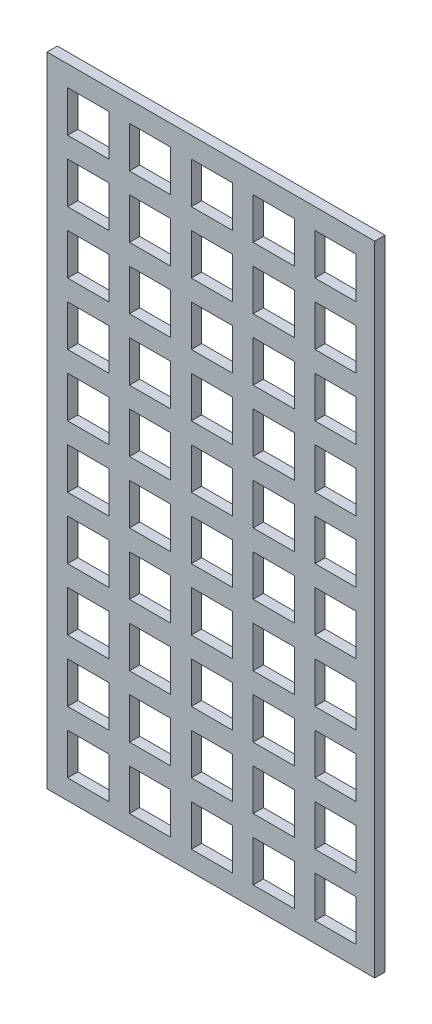
SolidWorks part; units mm, degrees
ref_plane "Front Plane" through (0, 0, 0) normal (0, 0, 1) x (1, 0, 0)
ref_plane "Top Plane" through (0, 0, 0) normal (0, 1, 0) x (1, 0, 0)
ref_plane "Right Plane" through (0, 0, 0) normal (1, 0, 0) x (0, 0, -1)
sketch "Sketch1" plane through (0, 0, 0) normal (0, 0, 1) x (1, 0, 0)
  line L0 (0, 0) -> (0, -5)
  line L1 (0, 0) -> (79.5, 0)
  line L2 (0, 0) -> (0, -154.8)
  line L3 (0, -154.8) -> (79.5, -154.8)
  line L4 (79.5, 0) -> (79.5, -154.8)
  line L5 (5, -5) -> (0, -5) construction
  line L6 (0, -5) -> (5, -5) construction
  line L7 (5, 0) -> (5, -5) construction
  line L8 (20, 0) -> (20, -5) construction
  line L9 (5, -5) -> (15, -5)
  line L10 (20, -15) -> (30, -15)
  line L11 (20, -15) -> (20, -5)
  line L12 (5, -15) -> (5, -5)
  line L13 (5, -15) -> (5, -5)
  line L14 (5, -5) -> (15, -5)
  line L15 (5, -5) -> (5, -15)
  line L16 (5, -15) -> (15, -15)
  line L17 (15, -5) -> (15, -15)
  line L18 (5, -5) -> (15, -5)
  line L19 (20, -5) -> (30, -5)
  line L20 (30, -5) -> (30, -15)
  line L21 (35, 0) -> (35, -5) construction
  line L22 (35, -15) -> (45, -15)
  line L23 (35, -15) -> (35, -5)
  line L24 (35, -5) -> (45, -5)
  line L25 (45, -5) -> (45, -15)
  line L26 (50, 0) -> (50, -5) construction
  line L27 (50, -15) -> (60, -15)
  line L28 (50, -15) -> (50, -5)
  line L29 (50, -5) -> (60, -5)
  line L30 (60, -5) -> (60, -15)
  line L31 (65, 0) -> (65, -5) construction
  line L32 (65, -15) -> (75, -15)
  line L33 (65, -15) -> (65, -5)
  line L34 (65, -5) -> (75, -5)
  line L35 (75, -5) -> (75, -15)
  line L36 (20, -15) -> (20, -20) construction
  line L37 (20, -30) -> (30, -30)
  line L38 (20, -30) -> (20, -20)
  line L39 (20, -20) -> (30, -20)
  line L40 (30, -20) -> (30, -30)
  line L41 (35, -15) -> (35, -20) construction
  line L42 (35, -30) -> (45, -30)
  line L43 (35, -30) -> (35, -20)
  line L44 (35, -20) -> (45, -20)
  line L45 (45, -20) -> (45, -30)
  line L46 (50, -15) -> (50, -20) construction
  line L47 (50, -30) -> (60, -30)
  line L48 (50, -30) -> (50, -20)
  line L49 (50, -20) -> (60, -20)
  line L50 (60, -20) -> (60, -30)
  line L51 (65, -15) -> (65, -20) construction
  line L52 (65, -30) -> (75, -30)
  line L53 (65, -30) -> (65, -20)
  line L54 (65, -20) -> (75, -20)
  line L55 (75, -20) -> (75, -30)
  line L56 (20, -30) -> (20, -35) construction
  line L57 (20, -45) -> (30, -45)
  line L58 (20, -45) -> (20, -35)
  line L59 (20, -35) -> (30, -35)
  line L60 (30, -35) -> (30, -45)
  line L61 (35, -30) -> (35, -35) construction
  line L62 (35, -45) -> (45, -45)
  line L63 (35, -45) -> (35, -35)
  line L64 (35, -35) -> (45, -35)
  line L65 (45, -35) -> (45, -45)
  line L66 (50, -30) -> (50, -35) construction
  line L67 (50, -45) -> (60, -45)
  line L68 (50, -45) -> (50, -35)
  line L69 (50, -35) -> (60, -35)
  line L70 (60, -35) -> (60, -45)
  line L71 (65, -30) -> (65, -35) construction
  line L72 (65, -45) -> (75, -45)
  line L73 (65, -45) -> (65, -35)
  line L74 (65, -35) -> (75, -35)
  line L75 (75, -35) -> (75, -45)
  line L76 (20, -45) -> (20, -50) construction
  line L77 (20, -60) -> (30, -60)
  line L78 (20, -60) -> (20, -50)
  line L79 (20, -50) -> (30, -50)
  line L80 (30, -50) -> (30, -60)
  line L81 (35, -45) -> (35, -50) construction
  line L82 (35, -60) -> (45, -60)
  line L83 (35, -60) -> (35, -50)
  line L84 (35, -50) -> (45, -50)
  line L85 (45, -50) -> (45, -60)
  line L86 (50, -45) -> (50, -50) construction
  line L87 (50, -60) -> (60, -60)
  line L88 (50, -60) -> (50, -50)
  line L89 (50, -50) -> (60, -50)
  line L90 (60, -50) -> (60, -60)
  line L91 (65, -45) -> (65, -50) construction
  line L92 (65, -60) -> (75, -60)
  line L93 (65, -60) -> (65, -50)
  line L94 (65, -50) -> (75, -50)
  line L95 (75, -50) -> (75, -60)
  line L96 (20, -60) -> (20, -65) construction
  line L97 (20, -75) -> (30, -75)
  line L98 (20, -75) -> (20, -65)
  line L99 (20, -65) -> (30, -65)
  line L100 (30, -65) -> (30, -75)
  line L101 (35, -60) -> (35, -65) construction
  line L102 (35, -75) -> (45, -75)
  line L103 (35, -75) -> (35, -65)
  line L104 (35, -65) -> (45, -65)
  line L105 (45, -65) -> (45, -75)
  line L106 (50, -60) -> (50, -65) construction
  line L107 (50, -75) -> (60, -75)
  line L108 (50, -75) -> (50, -65)
  line L109 (50, -65) -> (60, -65)
  line L110 (60, -65) -> (60, -75)
  line L111 (65, -60) -> (65, -65) construction
  line L112 (65, -75) -> (75, -75)
  line L113 (65, -75) -> (65, -65)
  line L114 (65, -65) -> (75, -65)
  line L115 (75, -65) -> (75, -75)
  line L116 (20, -75) -> (20, -80) construction
  line L117 (20, -90) -> (30, -90)
  line L118 (20, -90) -> (20, -80)
  line L119 (20, -80) -> (30, -80)
  line L120 (30, -80) -> (30, -90)
  line L121 (35, -75) -> (35, -80) construction
  line L122 (35, -90) -> (45, -90)
  line L123 (35, -90) -> (35, -80)
  line L124 (35, -80) -> (45, -80)
  line L125 (45, -80) -> (45, -90)
  line L126 (50, -75) -> (50, -80) construction
  line L127 (50, -90) -> (60, -90)
  line L128 (50, -90) -> (50, -80)
  line L129 (50, -80) -> (60, -80)
  line L130 (60, -80) -> (60, -90)
  line L131 (65, -75) -> (65, -80) construction
  line L132 (65, -90) -> (75, -90)
  line L133 (65, -90) -> (65, -80)
  line L134 (65, -80) -> (75, -80)
  line L135 (75, -80) -> (75, -90)
  line L136 (20, -90) -> (20, -95) construction
  line L137 (20, -105) -> (30, -105)
  line L138 (20, -105) -> (20, -95)
  line L139 (20, -95) -> (30, -95)
  line L140 (30, -95) -> (30, -105)
  line L141 (35, -90) -> (35, -95) construction
  line L142 (35, -105) -> (45, -105)
  line L143 (35, -105) -> (35, -95)
  line L144 (35, -95) -> (45, -95)
  line L145 (45, -95) -> (45, -105)
  line L146 (50, -90) -> (50, -95) construction
  line L147 (50, -105) -> (60, -105)
  line L148 (50, -105) -> (50, -95)
  line L149 (50, -95) -> (60, -95)
  line L150 (60, -95) -> (60, -105)
  line L151 (65, -90) -> (65, -95) construction
  line L152 (65, -105) -> (75, -105)
  line L153 (65, -105) -> (65, -95)
  line L154 (65, -95) -> (75, -95)
  line L155 (75, -95) -> (75, -105)
  line L156 (20, -105) -> (20, -110) construction
  line L157 (20, -120) -> (30, -120)
  line L158 (20, -120) -> (20, -110)
  line L159 (20, -110) -> (30, -110)
  line L160 (30, -110) -> (30, -120)
  line L161 (35, -105) -> (35, -110) construction
  line L162 (35, -120) -> (45, -120)
  line L163 (35, -120) -> (35, -110)
  line L164 (35, -110) -> (45, -110)
  line L165 (45, -110) -> (45, -120)
  line L166 (50, -105) -> (50, -110) construction
  line L167 (50, -120) -> (60, -120)
  line L168 (50, -120) -> (50, -110)
  line L169 (50, -110) -> (60, -110)
  line L170 (60, -110) -> (60, -120)
  line L171 (65, -105) -> (65, -110) construction
  line L172 (65, -120) -> (75, -120)
  line L173 (65, -120) -> (65, -110)
  line L174 (65, -110) -> (75, -110)
  line L175 (75, -110) -> (75, -120)
  line L176 (20, -120) -> (20, -125) construction
  line L177 (20, -135) -> (30, -135)
  line L178 (20, -135) -> (20, -125)
  line L179 (20, -125) -> (30, -125)
  line L180 (30, -125) -> (30, -135)
  line L181 (35, -120) -> (35, -125) construction
  line L182 (35, -135) -> (45, -135)
  line L183 (35, -135) -> (35, -125)
  line L184 (35, -125) -> (45, -125)
  line L185 (45, -125) -> (45, -135)
  line L186 (50, -120) -> (50, -125) construction
  line L187 (50, -135) -> (60, -135)
  line L188 (50, -135) -> (50, -125)
  line L189 (50, -125) -> (60, -125)
  line L190 (60, -125) -> (60, -135)
  line L191 (65, -120) -> (65, -125) construction
  line L192 (65, -135) -> (75, -135)
  line L193 (65, -135) -> (65, -125)
  line L194 (65, -125) -> (75, -125)
  line L195 (75, -125) -> (75, -135)
  line L196 (20, -135) -> (20, -140) construction
  line L197 (20, -150) -> (30, -150)
  line L198 (20, -150) -> (20, -140)
  line L199 (20, -140) -> (30, -140)
  line L200 (30, -140) -> (30, -150)
  line L201 (35, -135) -> (35, -140) construction
  line L202 (35, -150) -> (45, -150)
  line L203 (35, -150) -> (35, -140)
  line L204 (35, -140) -> (45, -140)
  line L205 (45, -140) -> (45, -150)
  line L206 (50, -135) -> (50, -140) construction
  line L207 (50, -150) -> (60, -150)
  line L208 (50, -150) -> (50, -140)
  line L209 (50, -140) -> (60, -140)
  line L210 (60, -140) -> (60, -150)
  line L211 (65, -135) -> (65, -140) construction
  line L212 (65, -150) -> (75, -150)
  line L213 (65, -150) -> (65, -140)
  line L214 (65, -140) -> (75, -140)
  line L215 (75, -140) -> (75, -150)
  line L216 (5, -15) -> (5, -20) construction
  line L217 (5, -30) -> (15, -30)
  line L218 (5, -30) -> (5, -20)
  line L219 (5, -20) -> (15, -20)
  line L220 (15, -20) -> (15, -30)
  line L221 (5, -30) -> (5, -35) construction
  line L222 (5, -45) -> (15, -45)
  line L223 (5, -45) -> (5, -35)
  line L224 (5, -35) -> (15, -35)
  line L225 (15, -35) -> (15, -45)
  line L226 (5, -45) -> (5, -50) construction
  line L227 (5, -60) -> (15, -60)
  line L228 (5, -60) -> (5, -50)
  line L229 (5, -50) -> (15, -50)
  line L230 (15, -50) -> (15, -60)
  line L231 (5, -60) -> (5, -65) construction
  line L232 (5, -75) -> (15, -75)
  line L233 (5, -75) -> (5, -65)
  line L234 (5, -65) -> (15, -65)
  line L235 (15, -65) -> (15, -75)
  line L236 (5, -75) -> (5, -80) construction
  line L237 (5, -90) -> (15, -90)
  line L238 (5, -90) -> (5, -80)
  line L239 (5, -80) -> (15, -80)
  line L240 (15, -80) -> (15, -90)
  line L241 (5, -90) -> (5, -95) construction
  line L242 (5, -105) -> (15, -105)
  line L243 (5, -105) -> (5, -95)
  line L244 (5, -95) -> (15, -95)
  line L245 (15, -95) -> (15, -105)
  line L246 (5, -105) -> (5, -110) construction
  line L247 (5, -120) -> (15, -120)
  line L248 (5, -120) -> (5, -110)
  line L249 (5, -110) -> (15, -110)
  line L250 (15, -110) -> (15, -120)
  line L251 (5, -120) -> (5, -125) construction
  line L252 (5, -135) -> (15, -135)
  line L253 (5, -135) -> (5, -125)
  line L254 (5, -125) -> (15, -125)
  line L255 (15, -125) -> (15, -135)
  line L256 (5, -135) -> (5, -140) construction
  line L257 (5, -150) -> (15, -150)
  line L258 (5, -150) -> (5, -140)
  line L259 (5, -140) -> (15, -140)
  line L260 (15, -140) -> (15, -150)
  point P8 (0, 0)
  dimension "D1" = 79.5
  dimension "D2" = 154.8
  dimension "D3" = 5
  dimension "D4" = 5
  dimension "D5" = 10
  dimension "D6" = 5
  dimension "D7" = 10
  dimension "D8" = 10
  dimension "D9" = 10
  dimension "D10" = 5
  dimension "D11" = 5
extrude "Boss-Extrude1" add sketch "Sketch1" along normal blind 2.5 contours L4 L1 L0 L2 L3 L9 L17 L16 L12 L19 L20 L10 L11 L24 L25 L22 L23 L29 L30 L27 L28 L34 L35 L32 L33 L39 L40 L37 L38 L44 L45 L42 L43 L49 L50 L47 L48 L54 L55 L52 L53
